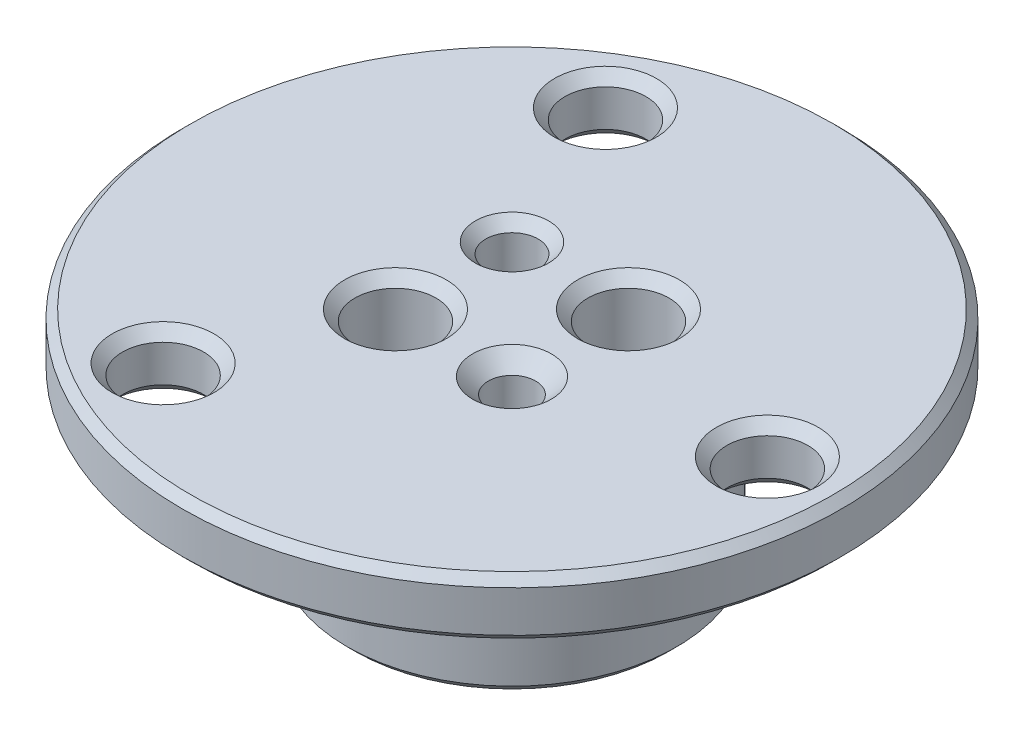
SolidWorks part; units mm, degrees
material "6061 Alloy"
ref_plane "Front" through (0, 0, 0) normal (0, 0, 1) x (1, 0, 0)
ref_plane "Top" through (0, 0, 0) normal (0, 1, 0) x (1, 0, 0)
ref_plane "Right" through (0, 0, 0) normal (1, 0, 0) x (0, 0, -1)
sketch "Sketch1" plane through (0, 0, 0) normal (1, 0, 0) x (0, 0, -1)
  line L0 (0, 0) -> (0, 13.2433)
  line L1 (0, 13.2433) -> (20, 13.2433)
  line L2 (20, 13.2433) -> (20, 9.7433)
  line L3 (20, 9.7433) -> (10, 9.7433)
  line L4 (10, 9.7433) -> (10, 0)
  line L5 (10, 0) -> (0, 0)
  line L6 (0, 0) -> (0, -21.9651) construction
  dimension "D1" = 20
  dimension "D2" = 40
  dimension "D3" = 9.7433
  dimension "D4" = 3.5
revolve "Revolve1" add sketch "Sketch1" angle 360 about L6
sketch "Sketch3" plane through (0, 13.2433, 0) normal (0, 1, 0) x (1, 0, 0)
  line L0 (-3.5355, -3.5355) -> (3.5355, 3.5355) construction
  line L1 (-3.5355, -3.5355) -> (3.5355, -3.5355)
  line L2 (-3.5355, -3.5355) -> (-3.5355, 3.5355)
  line L3 (-3.5355, 3.5355) -> (3.5355, 3.5355)
  line L4 (3.5355, -3.5355) -> (3.5355, 3.5355)
  line L7 (0, 0) -> (0, 3.5856) construction
  line L8 (0, 0) -> (10.0332, 0) construction
  point P4 (0, 0)
  point P9 (3.5355, 3.5355)
  point P11 (-3.5355, 3.5355)
  point P12 (3.5355, -3.5355)
  point P13 (-3.5355, -3.5355)
  dimension "D1" = 10
hole_wizard "#8 Clearance Hole2" positions "3DSketch1" profile "Sketch4" hole size "#8" standard "Ansi Inch" end condition through all
sketch3d "3DSketch1"
  point P0 (3.5355, 13.2433, -3.5355)
  point P3 (-3.5355, 13.2433, 3.5355)
sketch "Sketch4" plane through (3.5355, 13.2433, -3.5355) normal (1, 0, 0) x (0, 0, 1)
  line L0 (0, 0) -> (0, 13.2433)
  line L1 (0, 13.2433) -> (3.0924, 13.2433)
  line L2 (2.4574, 12.6083) -> (2.4574, 0.635)
  line L3 (2.4574, 0.635) -> (3.0924, 0)
  line L5 (3.0924, 0) -> (0, 0)
  line L6 (-2.4574, 0.635) -> (-3.0924, 0) construction
  line L7 (3.0924, 13.2433) -> (2.4574, 12.6083)
  line L8 (-3.0925, 13.2433) -> (-2.4575, 12.6083) construction
  line L11 (0, -6.35) -> (0, 107.95) construction
  dimension "Thru Hole Dia." = 4.9149
  dimension "Thru Hole Depth" = 13.2433
  dimension "Near C'Sink Dia." = 6.1849
  dimension "Near C'Sink Angle" = 90
  dimension "Far C'Sink Dia." = 6.1849
  dimension "Far C'Sink Angle" = 90
hole_wizard "1/8 (0.125) Diameter Hole1" positions "3DSketch2" profile "Sketch5" hole size "1/8" standard "Ansi Inch" end condition through all
sketch3d "3DSketch2"
  point P0 (-3.5355, 13.2433, -3.5355)
sketch "Sketch5" plane through (-3.5355, 13.2433, -3.5355) normal (1, 0, 0) x (0, 0, 1)
  line L0 (0, 0) -> (0, 13.2433)
  line L1 (0, 13.2433) -> (2.2225, 13.2433)
  line L2 (1.5875, 12.6083) -> (1.5875, 0.635)
  line L3 (1.5875, 0.635) -> (2.2225, 0)
  line L5 (2.2225, 0) -> (0, 0)
  line L6 (-1.5875, 0.635) -> (-2.2225, 0) construction
  line L7 (2.2225, 13.2433) -> (1.5875, 12.6083)
  line L8 (-2.2225, 13.2433) -> (-1.5875, 12.6083) construction
  line L11 (0, -6.35) -> (0, 107.95) construction
  dimension "Thru Hole Dia." = 3.175
  dimension "Thru Hole Depth" = 13.2433
  dimension "Near C'Sink Dia." = 4.445
  dimension "Near C'Sink Angle" = 90
  dimension "Far C'Sink Dia." = 4.445
  dimension "Far C'Sink Angle" = 90
sketch "Sketch6" plane through (0, 0, 0) normal (1, 0, 0) x (0, 0, -1)
  line L0 (0, 0) -> (0, -32.7024) construction
  line L1 (27.9827, 0) -> (17.5, 0)
  line L2 (27.9827, 0) -> (27.9827, 10)
  line L3 (27.9827, 10) -> (17.5, 10)
  line L4 (17.5, 0) -> (17.5, 10)
  line L8 (-10, 0) -> (10, 0) construction
  dimension "D1" = 35
  dimension "D2" = 10
  dimension "D3" = 10.4827
extrude "Extrude1" [suppressed] cut sketch "Sketch6" against normal through all and the other way through all
mirror "Mirror1" [suppressed] about plane through (0, 0, 0) normal (0, 0, 1)
sketch "Sketch7" plane through (0, 13.2433, 0) normal (0, 1, 0) x (1, 0, 0)
  line L0 (0, 0) -> (42.187, 0) construction
  line L1 (0, 0) -> (-21.1417, 36.6185) construction
  circle A3 centre (0, 0) radius 15.5
  point P0 (-7.75, 13.4234)
  point P2 (15.5, 0)
  point P8 (-7.75, -13.4234)
  dimension "D1" = 31
  dimension "D2" = 120
hole_wizard "#8 Clearance Hole1" positions "3DSketch3" profile "Sketch8" hole size "#8" standard "Ansi Inch" end condition up to next
sketch3d "3DSketch3"
  point P0 (-7.75, 13.2433, -13.4234)
  point P3 (15.5, 13.2433, 0)
  point P6 (-7.75, 13.2433, 13.4234)
sketch "Sketch8" plane through (-7.75, 13.2433, -13.4234) normal (1, 0, 0) x (0, 0, 1)
  line L0 (0, 0) -> (0, 3.5)
  line L1 (0, 3.5) -> (3.0861, 3.5)
  line L2 (2.4574, 2.8713) -> (2.4574, 0.635)
  line L3 (2.4574, 0.635) -> (3.0924, 0)
  line L5 (3.0924, 0) -> (0, 0)
  line L6 (-2.4574, 0.635) -> (-3.0924, 0) construction
  line L7 (3.0861, 3.5) -> (2.4574, 2.8713)
  line L8 (-3.0861, 3.5) -> (-2.4575, 2.8713) construction
  line L11 (0, -6.35) -> (0, 107.95) construction
  dimension "Thru Hole Dia." = 4.9149
  dimension "Thru Hole Depth" = 3.5
  dimension "Near C'Sink Dia." = 6.1849
  dimension "Near C'Sink Angle" = 90
  dimension "Far C'Sink Dia." = 6.1722
  dimension "Far C'Sink Angle" = 90
sketch "Sketch9" plane through (0, 13.2433, 0) normal (0, 1, 0) x (1, 0, 0)
  line L0 (-3.5355, 3.5355) -> (-3.5355, -3.5355) construction
  point P4 (-3.5355, -4.4645)
  dimension "D1" = 8
hole_wizard "#6-40 Tapped Hole1" positions "3DSketch4" profile "Sketch10" tap size "#6-40" standard "Ansi Inch" end condition through all
sketch3d "3DSketch4"
  point P0 (3.5355, 13.2433, 3.5355)
sketch "Sketch10" plane through (3.5355, 13.2433, 3.5355) normal (1, 0, 0) x (0, 0, 1)
  line L0 (0, 0) -> (0, 13.2433)
  line L1 (0, 13.2433) -> (2.3876, 13.2433)
  line L2 (1.4351, 12.2908) -> (1.4351, 0.9525)
  line L3 (1.4351, 0.9525) -> (2.3876, 0)
  line L5 (2.3876, 0) -> (0, 0)
  line L6 (-1.4351, 0.9525) -> (-2.3876, 0) construction
  line L7 (2.3876, 13.2433) -> (1.4351, 12.2908)
  line L8 (-2.3876, 13.2433) -> (-1.4351, 12.2908) construction
  line L11 (0, -6.35) -> (0, 107.95) construction
  dimension "Thru Tap Drill Dia." = 2.8702
  dimension "Thru Tap Drill Depth" = 13.2433
  dimension "Near C'Sink Dia." = 4.7752
  dimension "Near C'Sink Angle" = 90
  dimension "Far C'Sink Dia." = 4.7752
  dimension "Far C'Sink Angle" = 90
cosmetic thread "Hole Thread1" parameters "D2"=3.5052
chamfer "Chamfer1" distance 0.5 angle 45 3 edges at (0, 0, 10) (0, 9.7433, 20) (0, 13.2433, 20)
fillet "Fillet1" radius 0.5 1 edges at (0, 9.7433, 10)
